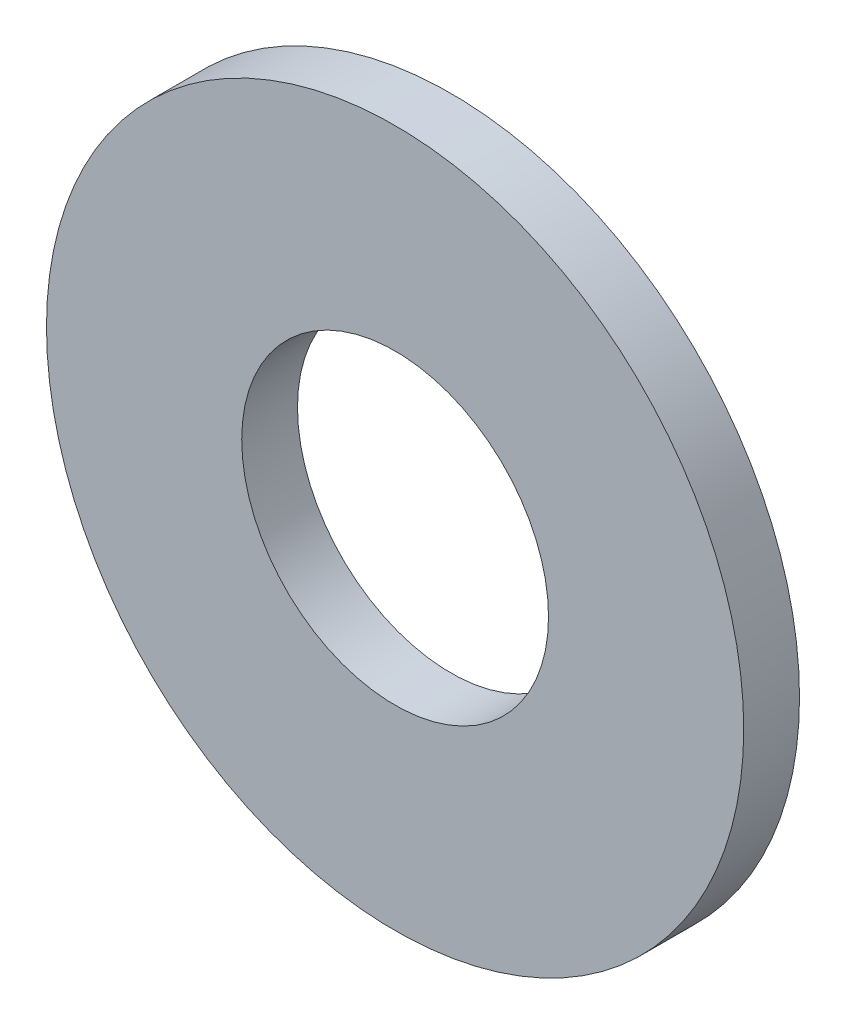
SolidWorks part; units mm, degrees
material "Alloy Steel (SS)"
ref_plane "Front Plane" through (0, 0, 0) normal (0, 0, 1) x (1, 0, 0)
ref_plane "Top Plane" through (0, 0, 0) normal (0, 1, 0) x (1, 0, 0)
ref_plane "Right Plane" through (0, 0, 0) normal (1, 0, 0) x (0, 0, -1)
sketch "Sketch1" plane through (0, 0, 0) normal (0, 0, 1) x (1, 0, 0)
  circle A0 centre (0, 0) radius 2.5
  circle A1 centre (0, 0) radius 1.1
  dimension "OD" = 5
  dimension "ID1" = 2.2
extrude "Boss-Extrude1" add sketch "Sketch1" along normal blind 0.4
